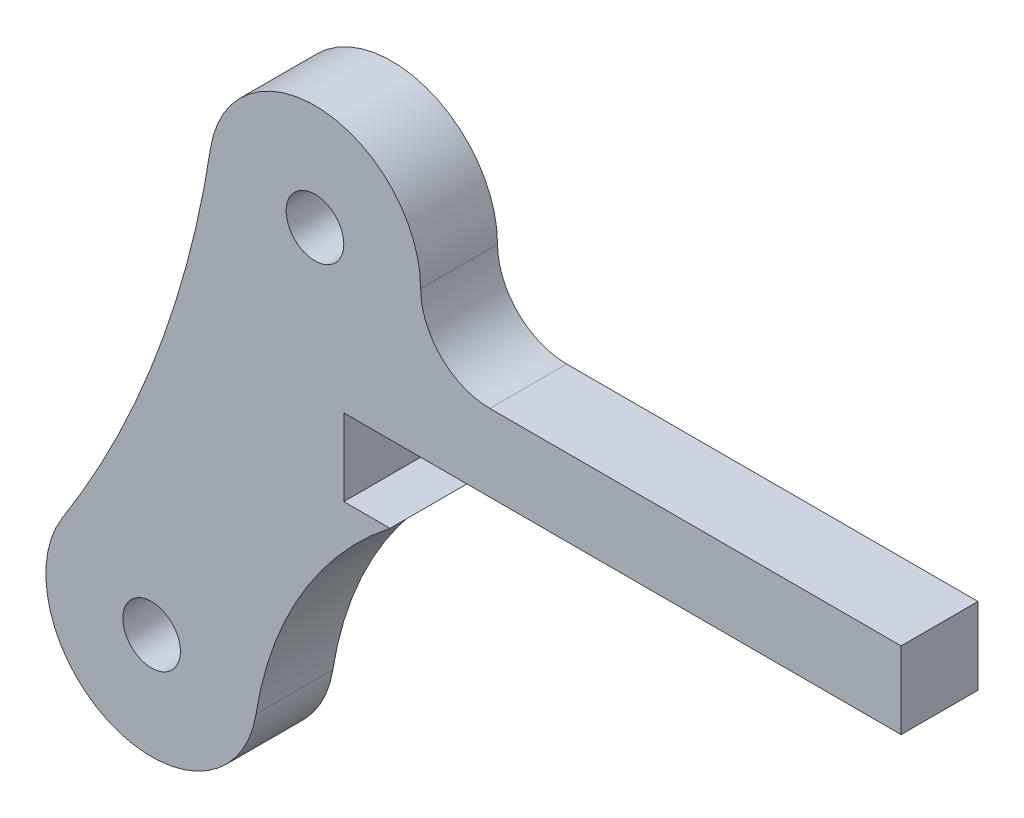
SolidWorks part; units mm, degrees
ref_plane "Front Plane" through (0, 0, 0) normal (0, 0, 1) x (1, 0, 0)
ref_plane "Top Plane" through (0, 0, 0) normal (0, 1, 0) x (1, 0, 0)
ref_plane "Right Plane" through (0, 0, 0) normal (1, 0, 0) x (0, 0, -1)
sketch "Sketch1" plane through (0, 0, 0) normal (0, 0, 1) x (1, 0, 0)
  line L0 (0, 0) -> (-8.5, -22.6) construction
  line L1 (9.1, -3.6) -> (30.5, -3.6)
  line L2 (15.5, -7.6) -> (30.5, -7.6)
  line L3 (30.5, -3.6) -> (30.5, -7.6)
  circle A0 centre (0, 0) radius 1.5
  circle A1 centre (0, 0) radius 5.5
  circle A2 centre (-8.5, -22.6) radius 1.5
  circle A3 centre (-8.5, -22.6) radius 5.5
  arc A4 (-5.4354, 0.8404) -> (-13.142, -19.6502) centre (-58.2341, 9.0037) cw
  arc A5 (5.5, 0) -> (9.1, -3.6) centre (9.1, 0) ccw
  arc A6 (-3.0676, -23.4598) -> (15.5, -7.6) centre (15.5, -26.3988) cw
  point P7 (-8.228, -9.8039)
  point P17 (17.4218, -11.2452)
  point P18 (0, 0)
  point P19 (23.6679, -7.6)
  point P20 (18.1713, -7.6)
  dimension "D1" = 4
  dimension "D2" = 3
  dimension "D4" = 8.5
  dimension "D7" = 4.25
  dimension "D8" = 15
  dimension "D3" = 22.6
  dimension "D5" = 4
  dimension "D6" = 25
  dimension "D9" = 15
extrude "Boss-Extrude1" add sketch "Sketch1" along normal blind 4
sketch "Sketch2" plane through (0, 0, 4) normal (0, 0, 1) x (1, 0, 0)
  line L0 (30.5, -3.6) -> (30.5, -7.6) construction
  line L1 (1.5, -7.6) -> (30.5, -7.6)
  line L2 (1.5, -7.6) -> (1.5, -11.6)
  line L3 (1.5, -11.6) -> (30.5, -11.6)
  line L4 (30.5, -7.6) -> (30.5, -11.6)
  line L5 (15.5, -7.6) -> (30.5, -7.6) construction
  circle A0 centre (0, 0) radius 1.5 construction
extrude "Cut-Extrude1" cut sketch "Sketch2" against normal blind 10
